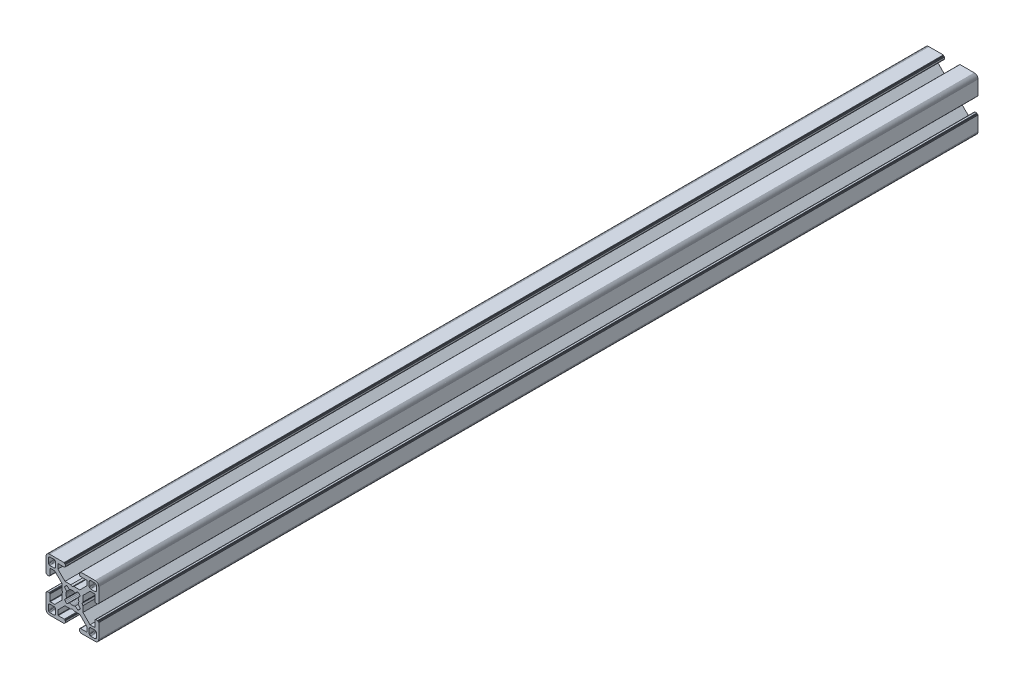
SolidWorks part; units mm, degrees
ref_plane "Front Plane" through (0, 0, 0) normal (0, 0, 1) x (1, 0, 0)
ref_plane "Top Plane" through (0, 0, 0) normal (0, 1, 0) x (1, 0, 0)
ref_plane "Right Plane" through (0, 0, 0) normal (1, 0, 0) x (0, 0, -1)
ref_plane "Plane1" through (0, 0, 0) normal (0, 0, 1) x (1, 0, 0)
sketch "Sketch1" plane through (0, 0, 0) normal (0, 0, 1) x (1, 0, 0)
  line L0 (28.3473, 29.9696) -> (28, 30)
  line L1 (28, 30) -> (19.75, 30)
  line L2 (19.75, 30) -> (19.7153, 29.997)
  line L3 (19.7153, 29.997) -> (19.6816, 29.9879)
  line L4 (19.6816, 29.9879) -> (19.65, 29.9732)
  line L5 (19.65, 29.9732) -> (19.6214, 29.9532)
  line L6 (19.6214, 29.9532) -> (19.5968, 29.9286)
  line L7 (19.5968, 29.9286) -> (19.5768, 29.9)
  line L8 (19.5768, 29.9) -> (19.5621, 29.8684)
  line L9 (19.5621, 29.8684) -> (19.553, 29.8347)
  line L10 (19.553, 29.8347) -> (19.55, 29.8)
  line L11 (19.55, 29.8) -> (19.55, 29.7)
  line L12 (19.55, 29.7) -> (19.547, 29.6653)
  line L13 (19.547, 29.6653) -> (19.5379, 29.6316)
  line L14 (19.5379, 29.6316) -> (19.5232, 29.6)
  line L15 (19.5232, 29.6) -> (19.5032, 29.5714)
  line L16 (19.5032, 29.5714) -> (19.4786, 29.5468)
  line L17 (19.4786, 29.5468) -> (19.45, 29.5268)
  line L18 (19.45, 29.5268) -> (19.4184, 29.5121)
  line L19 (19.4184, 29.5121) -> (19.3847, 29.503)
  line L20 (19.3847, 29.503) -> (19.35, 29.5)
  line L21 (19.35, 29.5) -> (19.25, 29.5)
  line L22 (19.25, 29.5) -> (19.2153, 29.497)
  line L23 (19.2153, 29.497) -> (19.1816, 29.4879)
  line L24 (19.1816, 29.4879) -> (19.15, 29.4732)
  line L25 (19.15, 29.4732) -> (19.1214, 29.4532)
  line L26 (19.1214, 29.4532) -> (19.0968, 29.4286)
  line L27 (19.0968, 29.4286) -> (19.0768, 29.4)
  line L28 (19.0768, 29.4) -> (19.0621, 29.3684)
  line L29 (19.0621, 29.3684) -> (19.053, 29.3347)
  line L30 (19.053, 29.3347) -> (19.05, 29.3)
  line L31 (19.05, 29.3) -> (19.05, 28.4)
  line L32 (19.05, 28.4) -> (19.0591, 28.2958)
  line L33 (19.0591, 28.2958) -> (19.0862, 28.1948)
  line L34 (19.0862, 28.1948) -> (19.1304, 28.1)
  line L35 (19.1304, 28.1) -> (19.1904, 28.0143)
  line L36 (19.1904, 28.0143) -> (19.2643, 27.9404)
  line L37 (19.2643, 27.9404) -> (19.35, 27.8804)
  line L38 (19.35, 27.8804) -> (19.4448, 27.8362)
  line L39 (19.4448, 27.8362) -> (19.5458, 27.8091)
  line L40 (19.5458, 27.8091) -> (19.65, 27.8)
  line L41 (19.65, 27.8) -> (23.05, 27.8)
  line L42 (23.05, 27.8) -> (23.0847, 27.7969)
  line L43 (23.0847, 27.7969) -> (23.1184, 27.7879)
  line L44 (23.1184, 27.7879) -> (23.15, 27.7732)
  line L45 (23.15, 27.7732) -> (23.1786, 27.7532)
  line L46 (23.1786, 27.7532) -> (23.2032, 27.7285)
  line L47 (23.2032, 27.7285) -> (23.2232, 27.7)
  line L48 (23.2232, 27.7) -> (23.2379, 27.6684)
  line L49 (23.2379, 27.6684) -> (23.247, 27.6347)
  line L50 (23.247, 27.6347) -> (23.25, 27.6)
  line L51 (23.25, 27.6) -> (23.25, 25.05)
  line L52 (23.25, 25.05) -> (19.2045, 21)
  line L53 (19.2045, 21) -> (15.9, 21)
  line L54 (15.9, 21) -> (15, 20.4848)
  line L55 (15, 20.4848) -> (14.1, 21)
  line L56 (14.1, 21) -> (10.7955, 21)
  line L57 (10.7955, 21) -> (7.9973, 23.8013)
  line L58 (7.9973, 23.8013) -> (6.75, 25.05)
  line L59 (6.75, 25.05) -> (6.75, 27.6)
  line L60 (6.75, 27.6) -> (6.753, 27.6347)
  line L61 (6.753, 27.6347) -> (6.7621, 27.6684)
  line L62 (6.7621, 27.6684) -> (6.7768, 27.7)
  line L63 (6.7768, 27.7) -> (6.7968, 27.7285)
  line L64 (6.7968, 27.7285) -> (6.8215, 27.7532)
  line L65 (6.8215, 27.7532) -> (6.85, 27.7732)
  line L66 (6.85, 27.7732) -> (6.8816, 27.7879)
  line L67 (6.8816, 27.7879) -> (6.9153, 27.7969)
  line L68 (6.9153, 27.7969) -> (6.95, 27.8)
  line L69 (6.95, 27.8) -> (10.35, 27.8)
  line L70 (10.35, 27.8) -> (10.4542, 27.8091)
  line L71 (10.4542, 27.8091) -> (10.5552, 27.8362)
  line L72 (10.5552, 27.8362) -> (10.65, 27.8804)
  line L73 (10.65, 27.8804) -> (10.7357, 27.9404)
  line L74 (10.7357, 27.9404) -> (10.8096, 28.0143)
  line L75 (10.8096, 28.0143) -> (10.8696, 28.1)
  line L76 (10.8696, 28.1) -> (10.9138, 28.1948)
  line L77 (10.9138, 28.1948) -> (10.9409, 28.2958)
  line L78 (10.9409, 28.2958) -> (10.95, 28.4)
  line L79 (10.95, 28.4) -> (10.95, 29.3)
  line L80 (10.95, 29.3) -> (10.947, 29.3347)
  line L81 (10.947, 29.3347) -> (10.938, 29.3684)
  line L82 (10.938, 29.3684) -> (10.9232, 29.4)
  line L83 (10.9232, 29.4) -> (10.9032, 29.4286)
  line L84 (10.9032, 29.4286) -> (10.8786, 29.4532)
  line L85 (10.8786, 29.4532) -> (10.85, 29.4732)
  line L86 (10.85, 29.4732) -> (10.8184, 29.4879)
  line L87 (10.8184, 29.4879) -> (10.7847, 29.497)
  line L88 (10.7847, 29.497) -> (10.75, 29.5)
  line L89 (10.75, 29.5) -> (10.65, 29.5)
  line L90 (10.65, 29.5) -> (10.6153, 29.503)
  line L91 (10.6153, 29.503) -> (10.5816, 29.5121)
  line L92 (10.5816, 29.5121) -> (10.55, 29.5268)
  line L93 (10.55, 29.5268) -> (10.5214, 29.5468)
  line L94 (10.5214, 29.5468) -> (10.4968, 29.5714)
  line L95 (10.4968, 29.5714) -> (10.4768, 29.6)
  line L96 (10.4768, 29.6) -> (10.4621, 29.6316)
  line L97 (10.4621, 29.6316) -> (10.453, 29.6653)
  line L98 (10.453, 29.6653) -> (10.45, 29.7)
  line L99 (10.45, 29.7) -> (10.45, 29.8)
  line L100 (10.45, 29.8) -> (10.447, 29.8347)
  line L101 (10.447, 29.8347) -> (10.4379, 29.8684)
  line L102 (10.4379, 29.8684) -> (10.4232, 29.9)
  line L103 (10.4232, 29.9) -> (10.4032, 29.9286)
  line L104 (10.4032, 29.9286) -> (10.3786, 29.9532)
  line L105 (10.3786, 29.9532) -> (10.35, 29.9732)
  line L106 (10.35, 29.9732) -> (10.3184, 29.9879)
  line L107 (10.3184, 29.9879) -> (10.2847, 29.997)
  line L108 (10.2847, 29.997) -> (10.25, 30)
  line L109 (10.25, 30) -> (2, 30)
  line L110 (2, 30) -> (1.6527, 29.9696)
  line L111 (1.6527, 29.9696) -> (1.316, 29.8794)
  line L112 (1.316, 29.8794) -> (1, 29.7321)
  line L113 (1, 29.7321) -> (0.7144, 29.5321)
  line L114 (0.7144, 29.5321) -> (0.4679, 29.2856)
  line L115 (0.4679, 29.2856) -> (0.2679, 29)
  line L116 (0.2679, 29) -> (0.1206, 28.684)
  line L117 (0.1206, 28.684) -> (0.0304, 28.3473)
  line L118 (0.0304, 28.3473) -> (0, 28)
  line L119 (0, 28) -> (0, 19.75)
  line L120 (0, 19.75) -> (0.003, 19.7153)
  line L121 (0.003, 19.7153) -> (0.0121, 19.6816)
  line L122 (0.0121, 19.6816) -> (0.0268, 19.65)
  line L123 (0.0268, 19.65) -> (0.0468, 19.6214)
  line L124 (0.0468, 19.6214) -> (0.0714, 19.5968)
  line L125 (0.0714, 19.5968) -> (0.1, 19.5768)
  line L126 (0.1, 19.5768) -> (0.1316, 19.5621)
  line L127 (0.1316, 19.5621) -> (0.1653, 19.553)
  line L128 (0.1653, 19.553) -> (0.2, 19.55)
  line L129 (0.2, 19.55) -> (0.3, 19.55)
  line L130 (0.3, 19.55) -> (0.3347, 19.547)
  line L131 (0.3347, 19.547) -> (0.3684, 19.5379)
  line L132 (0.3684, 19.5379) -> (0.4, 19.5232)
  line L133 (0.4, 19.5232) -> (0.4286, 19.5032)
  line L134 (0.4286, 19.5032) -> (0.4532, 19.4786)
  line L135 (0.4532, 19.4786) -> (0.4732, 19.45)
  line L136 (0.4732, 19.45) -> (0.4879, 19.4184)
  line L137 (0.4879, 19.4184) -> (0.497, 19.3847)
  line L138 (0.497, 19.3847) -> (0.5, 19.35)
  line L139 (0.5, 19.35) -> (0.5, 19.25)
  line L140 (0.5, 19.25) -> (0.503, 19.2153)
  line L141 (0.503, 19.2153) -> (0.5121, 19.1816)
  line L142 (0.5121, 19.1816) -> (0.5268, 19.15)
  line L143 (0.5268, 19.15) -> (0.5468, 19.1214)
  line L144 (0.5468, 19.1214) -> (0.5714, 19.0968)
  line L145 (0.5714, 19.0968) -> (0.6, 19.0768)
  line L146 (0.6, 19.0768) -> (0.6316, 19.0621)
  line L147 (0.6316, 19.0621) -> (0.6653, 19.053)
  line L148 (0.6653, 19.053) -> (0.7, 19.05)
  line L149 (0.7, 19.05) -> (1.6, 19.05)
  line L150 (1.6, 19.05) -> (1.7042, 19.0591)
  line L151 (1.7042, 19.0591) -> (1.8052, 19.0862)
  line L152 (1.8052, 19.0862) -> (1.9, 19.1304)
  line L153 (1.9, 19.1304) -> (1.9857, 19.1904)
  line L154 (1.9857, 19.1904) -> (2.0596, 19.2643)
  line L155 (2.0596, 19.2643) -> (2.1196, 19.35)
  line L156 (2.1196, 19.35) -> (2.1638, 19.4448)
  line L157 (2.1638, 19.4448) -> (2.1909, 19.5458)
  line L158 (2.1909, 19.5458) -> (2.2, 19.65)
  line L159 (2.2, 19.65) -> (2.2, 23.05)
  line L160 (2.2, 23.05) -> (2.203, 23.0847)
  line L161 (2.203, 23.0847) -> (2.2121, 23.1184)
  line L162 (2.2121, 23.1184) -> (2.2268, 23.15)
  line L163 (2.2268, 23.15) -> (2.2468, 23.1786)
  line L164 (2.2468, 23.1786) -> (2.2714, 23.2032)
  line L165 (2.2714, 23.2032) -> (2.3, 23.2232)
  line L166 (2.3, 23.2232) -> (2.3316, 23.2379)
  line L167 (2.3316, 23.2379) -> (2.3653, 23.247)
  line L168 (2.3653, 23.247) -> (2.4, 23.25)
  line L169 (2.4, 23.25) -> (4.95, 23.25)
  line L170 (4.95, 23.25) -> (7.9973, 20.2027)
  line L171 (7.9973, 20.2027) -> (8.9955, 19.2045)
  line L172 (8.9955, 19.2045) -> (8.9955, 15.9)
  line L173 (8.9955, 15.9) -> (9.5151, 15)
  line L174 (9.5151, 15) -> (8.9955, 14.1)
  line L175 (8.9955, 14.1) -> (8.9955, 10.7955)
  line L176 (8.9955, 10.7955) -> (4.95, 6.75)
  line L177 (4.95, 6.75) -> (2.4, 6.75)
  line L178 (2.4, 6.75) -> (2.3653, 6.753)
  line L179 (2.3653, 6.753) -> (2.3316, 6.7621)
  line L180 (2.3316, 6.7621) -> (2.3, 6.7768)
  line L181 (2.3, 6.7768) -> (2.2714, 6.7968)
  line L182 (2.2714, 6.7968) -> (2.2468, 6.8214)
  line L183 (2.2468, 6.8214) -> (2.2268, 6.85)
  line L184 (2.2268, 6.85) -> (2.2121, 6.8816)
  line L185 (2.2121, 6.8816) -> (2.203, 6.9153)
  line L186 (2.203, 6.9153) -> (2.2, 6.95)
  line L187 (2.2, 6.95) -> (2.2, 10.35)
  line L188 (2.2, 10.35) -> (2.1909, 10.4542)
  line L189 (2.1909, 10.4542) -> (2.1638, 10.5552)
  line L190 (2.1638, 10.5552) -> (2.1196, 10.65)
  line L191 (2.1196, 10.65) -> (2.0596, 10.7357)
  line L192 (2.0596, 10.7357) -> (1.9857, 10.8096)
  line L193 (1.9857, 10.8096) -> (1.9, 10.8696)
  line L194 (1.9, 10.8696) -> (1.8052, 10.9138)
  line L195 (1.8052, 10.9138) -> (1.7042, 10.9409)
  line L196 (1.7042, 10.9409) -> (1.6, 10.95)
  line L197 (1.6, 10.95) -> (0.7, 10.95)
  line L198 (0.7, 10.95) -> (0.6653, 10.9469)
  line L199 (0.6653, 10.9469) -> (0.6316, 10.9379)
  line L200 (0.6316, 10.9379) -> (0.6, 10.9232)
  line L201 (0.6, 10.9232) -> (0.5715, 10.9032)
  line L202 (0.5715, 10.9032) -> (0.5468, 10.8785)
  line L203 (0.5468, 10.8785) -> (0.5268, 10.85)
  line L204 (0.5268, 10.85) -> (0.5121, 10.8184)
  line L205 (0.5121, 10.8184) -> (0.503, 10.7847)
  line L206 (0.503, 10.7847) -> (0.5, 10.75)
  line L207 (0.5, 10.75) -> (0.5, 10.65)
  line L208 (0.5, 10.65) -> (0.497, 10.6153)
  line L209 (0.497, 10.6153) -> (0.4879, 10.5816)
  line L210 (0.4879, 10.5816) -> (0.4732, 10.55)
  line L211 (0.4732, 10.55) -> (0.4532, 10.5214)
  line L212 (0.4532, 10.5214) -> (0.4286, 10.4968)
  line L213 (0.4286, 10.4968) -> (0.4, 10.4768)
  line L214 (0.4, 10.4768) -> (0.3684, 10.4621)
  line L215 (0.3684, 10.4621) -> (0.3347, 10.453)
  line L216 (0.3347, 10.453) -> (0.3, 10.45)
  line L217 (0.3, 10.45) -> (0.2, 10.45)
  line L218 (0.2, 10.45) -> (0.1653, 10.447)
  line L219 (0.1653, 10.447) -> (0.1316, 10.4379)
  line L220 (0.1316, 10.4379) -> (0.1, 10.4232)
  line L221 (0.1, 10.4232) -> (0.0714, 10.4032)
  line L222 (0.0714, 10.4032) -> (0.0468, 10.3786)
  line L223 (0.0468, 10.3786) -> (0.0268, 10.35)
  line L224 (0.0268, 10.35) -> (0.0121, 10.3184)
  line L225 (0.0121, 10.3184) -> (0.003, 10.2847)
  line L226 (0.003, 10.2847) -> (0, 10.25)
  line L227 (0, 10.25) -> (0, 2)
  line L228 (0, 2) -> (0.0304, 1.6527)
  line L229 (0.0304, 1.6527) -> (0.1206, 1.316)
  line L230 (0.1206, 1.316) -> (0.2679, 1)
  line L231 (0.2679, 1) -> (0.4679, 0.7144)
  line L232 (0.4679, 0.7144) -> (0.7144, 0.4679)
  line L233 (0.7144, 0.4679) -> (1, 0.2679)
  line L234 (1, 0.2679) -> (1.316, 0.1206)
  line L235 (1.316, 0.1206) -> (1.6527, 0.0304)
  line L236 (1.6527, 0.0304) -> (2, 0)
  line L237 (2, 0) -> (10.25, 0)
  line L238 (10.25, 0) -> (10.2847, 0.003)
  line L239 (10.2847, 0.003) -> (10.3184, 0.0121)
  line L240 (10.3184, 0.0121) -> (10.35, 0.0268)
  line L241 (10.35, 0.0268) -> (10.3786, 0.0468)
  line L242 (10.3786, 0.0468) -> (10.4032, 0.0714)
  line L243 (10.4032, 0.0714) -> (10.4232, 0.1)
  line L244 (10.4232, 0.1) -> (10.4379, 0.1316)
  line L245 (10.4379, 0.1316) -> (10.447, 0.1653)
  line L246 (10.447, 0.1653) -> (10.45, 0.2)
  line L247 (10.45, 0.2) -> (10.45, 0.3)
  line L248 (10.45, 0.3) -> (10.453, 0.3347)
  line L249 (10.453, 0.3347) -> (10.4621, 0.3684)
  line L250 (10.4621, 0.3684) -> (10.4768, 0.4)
  line L251 (10.4768, 0.4) -> (10.4968, 0.4286)
  line L252 (10.4968, 0.4286) -> (10.5214, 0.4532)
  line L253 (10.5214, 0.4532) -> (10.55, 0.4732)
  line L254 (10.55, 0.4732) -> (10.5816, 0.4879)
  line L255 (10.5816, 0.4879) -> (10.6153, 0.497)
  line L256 (10.6153, 0.497) -> (10.65, 0.5)
  line L257 (10.65, 0.5) -> (10.75, 0.5)
  line L258 (10.75, 0.5) -> (10.7847, 0.503)
  line L259 (10.7847, 0.503) -> (10.8184, 0.5121)
  line L260 (10.8184, 0.5121) -> (10.85, 0.5268)
  line L261 (10.85, 0.5268) -> (10.8785, 0.5468)
  line L262 (10.8785, 0.5468) -> (10.9032, 0.5715)
  line L263 (10.9032, 0.5715) -> (10.9232, 0.6)
  line L264 (10.9232, 0.6) -> (10.9379, 0.6316)
  line L265 (10.9379, 0.6316) -> (10.9469, 0.6653)
  line L266 (10.9469, 0.6653) -> (10.95, 0.7)
  line L267 (10.95, 0.7) -> (10.95, 1.6)
  line L268 (10.95, 1.6) -> (10.9409, 1.7042)
  line L269 (10.9409, 1.7042) -> (10.9138, 1.8052)
  line L270 (10.9138, 1.8052) -> (10.8696, 1.9)
  line L271 (10.8696, 1.9) -> (10.8096, 1.9857)
  line L272 (10.8096, 1.9857) -> (10.7357, 2.0596)
  line L273 (10.7357, 2.0596) -> (10.65, 2.1196)
  line L274 (10.65, 2.1196) -> (10.5552, 2.1638)
  line L275 (10.5552, 2.1638) -> (10.4542, 2.1909)
  line L276 (10.4542, 2.1909) -> (10.35, 2.2)
  line L277 (10.35, 2.2) -> (6.95, 2.2)
  line L278 (6.95, 2.2) -> (6.9153, 2.203)
  line L279 (6.9153, 2.203) -> (6.8816, 2.212)
  line L280 (6.8816, 2.212) -> (6.85, 2.2268)
  line L281 (6.85, 2.2268) -> (6.8215, 2.2468)
  line L282 (6.8215, 2.2468) -> (6.7968, 2.2714)
  line L283 (6.7968, 2.2714) -> (6.7768, 2.3)
  line L284 (6.7768, 2.3) -> (6.7621, 2.3316)
  line L285 (6.7621, 2.3316) -> (6.753, 2.3653)
  line L286 (6.753, 2.3653) -> (6.75, 2.4)
  line L287 (6.75, 2.4) -> (6.75, 4.95)
  line L288 (6.75, 4.95) -> (9.7875, 7.9908)
  line L289 (9.7875, 7.9908) -> (10.7955, 9)
  line L290 (10.7955, 9) -> (14.1, 9)
  line L291 (14.1, 9) -> (15, 9.5151)
  line L292 (15, 9.5151) -> (15.9, 9)
  line L293 (15.9, 9) -> (19.2045, 9)
  line L294 (19.2045, 9) -> (20.2126, 7.9908)
  line L295 (20.2126, 7.9908) -> (23.25, 4.95)
  line L296 (23.25, 4.95) -> (23.25, 2.4)
  line L297 (23.25, 2.4) -> (23.247, 2.3653)
  line L298 (23.247, 2.3653) -> (23.2379, 2.3316)
  line L299 (23.2379, 2.3316) -> (23.2232, 2.3)
  line L300 (23.2232, 2.3) -> (23.2032, 2.2714)
  line L301 (23.2032, 2.2714) -> (23.1786, 2.2468)
  line L302 (23.1786, 2.2468) -> (23.15, 2.2268)
  line L303 (23.15, 2.2268) -> (23.1184, 2.212)
  line L304 (23.1184, 2.212) -> (23.0847, 2.203)
  line L305 (23.0847, 2.203) -> (23.05, 2.2)
  line L306 (23.05, 2.2) -> (19.65, 2.2)
  line L307 (19.65, 2.2) -> (19.5458, 2.1909)
  line L308 (19.5458, 2.1909) -> (19.4448, 2.1638)
  line L309 (19.4448, 2.1638) -> (19.35, 2.1196)
  line L310 (19.35, 2.1196) -> (19.2643, 2.0596)
  line L311 (19.2643, 2.0596) -> (19.1904, 1.9857)
  line L312 (19.1904, 1.9857) -> (19.1304, 1.9)
  line L313 (19.1304, 1.9) -> (19.0862, 1.8052)
  line L314 (19.0862, 1.8052) -> (19.0591, 1.7042)
  line L315 (19.0591, 1.7042) -> (19.05, 1.6)
  line L316 (19.05, 1.6) -> (19.05, 0.7)
  line L317 (19.05, 0.7) -> (19.053, 0.6653)
  line L318 (19.053, 0.6653) -> (19.0621, 0.6316)
  line L319 (19.0621, 0.6316) -> (19.0768, 0.6)
  line L320 (19.0768, 0.6) -> (19.0968, 0.5714)
  line L321 (19.0968, 0.5714) -> (19.1214, 0.5468)
  line L322 (19.1214, 0.5468) -> (19.15, 0.5268)
  line L323 (19.15, 0.5268) -> (19.1816, 0.5121)
  line L324 (19.1816, 0.5121) -> (19.2153, 0.503)
  line L325 (19.2153, 0.503) -> (19.25, 0.5)
  line L326 (19.25, 0.5) -> (19.35, 0.5)
  line L327 (19.35, 0.5) -> (19.3847, 0.497)
  line L328 (19.3847, 0.497) -> (19.4184, 0.4879)
  line L329 (19.4184, 0.4879) -> (19.45, 0.4732)
  line L330 (19.45, 0.4732) -> (19.4786, 0.4532)
  line L331 (19.4786, 0.4532) -> (19.5032, 0.4286)
  line L332 (19.5032, 0.4286) -> (19.5232, 0.4)
  line L333 (19.5232, 0.4) -> (19.5379, 0.3684)
  line L334 (19.5379, 0.3684) -> (19.547, 0.3347)
  line L335 (19.547, 0.3347) -> (19.55, 0.3)
  line L336 (19.55, 0.3) -> (19.55, 0.2)
  line L337 (19.55, 0.2) -> (19.553, 0.1653)
  line L338 (19.553, 0.1653) -> (19.5621, 0.1316)
  line L339 (19.5621, 0.1316) -> (19.5768, 0.1)
  line L340 (19.5768, 0.1) -> (19.5968, 0.0714)
  line L341 (19.5968, 0.0714) -> (19.6214, 0.0468)
  line L342 (19.6214, 0.0468) -> (19.65, 0.0268)
  line L343 (19.65, 0.0268) -> (19.6816, 0.0121)
  line L344 (19.6816, 0.0121) -> (19.7153, 0.003)
  line L345 (19.7153, 0.003) -> (19.75, 0)
  line L346 (19.75, 0) -> (28, 0)
  line L347 (28, 0) -> (28.3473, 0.0304)
  line L348 (28.3473, 0.0304) -> (28.684, 0.1206)
  line L349 (28.684, 0.1206) -> (29, 0.2679)
  line L350 (29, 0.2679) -> (29.2856, 0.4679)
  line L351 (29.2856, 0.4679) -> (29.5321, 0.7144)
  line L352 (29.5321, 0.7144) -> (29.7321, 1)
  line L353 (29.7321, 1) -> (29.8794, 1.316)
  line L354 (29.8794, 1.316) -> (29.9696, 1.6527)
  line L355 (29.9696, 1.6527) -> (30, 2)
  line L356 (30, 2) -> (30, 10.25)
  line L357 (30, 10.25) -> (29.997, 10.2847)
  line L358 (29.997, 10.2847) -> (29.988, 10.3184)
  line L359 (29.988, 10.3184) -> (29.9732, 10.35)
  line L360 (29.9732, 10.35) -> (29.9532, 10.3785)
  line L361 (29.9532, 10.3785) -> (29.9286, 10.4032)
  line L362 (29.9286, 10.4032) -> (29.9, 10.4232)
  line L363 (29.9, 10.4232) -> (29.8684, 10.4379)
  line L364 (29.8684, 10.4379) -> (29.8347, 10.447)
  line L365 (29.8347, 10.447) -> (29.8, 10.45)
  line L366 (29.8, 10.45) -> (29.7, 10.45)
  line L367 (29.7, 10.45) -> (29.6649, 10.4534)
  line L368 (29.6649, 10.4534) -> (29.6312, 10.4624)
  line L369 (29.6312, 10.4624) -> (29.5996, 10.4772)
  line L370 (29.5996, 10.4772) -> (29.5711, 10.4972)
  line L371 (29.5711, 10.4972) -> (29.5464, 10.5218)
  line L372 (29.5464, 10.5218) -> (29.5264, 10.5504)
  line L373 (29.5264, 10.5504) -> (29.5117, 10.582)
  line L374 (29.5117, 10.582) -> (29.5027, 10.6156)
  line L375 (29.5027, 10.6156) -> (29.4996, 10.6504)
  line L376 (29.4996, 10.6504) -> (29.4996, 10.7504)
  line L377 (29.4996, 10.7504) -> (29.497, 10.7847)
  line L378 (29.497, 10.7847) -> (29.4879, 10.8184)
  line L379 (29.4879, 10.8184) -> (29.4732, 10.85)
  line L380 (29.4732, 10.85) -> (29.4532, 10.8785)
  line L381 (29.4532, 10.8785) -> (29.4286, 10.9032)
  line L382 (29.4286, 10.9032) -> (29.4, 10.9232)
  line L383 (29.4, 10.9232) -> (29.3684, 10.9379)
  line L384 (29.3684, 10.9379) -> (29.3347, 10.9469)
  line L385 (29.3347, 10.9469) -> (29.3, 10.95)
  line L386 (29.3, 10.95) -> (28.4, 10.95)
  line L387 (28.4, 10.95) -> (28.2958, 10.9409)
  line L388 (28.2958, 10.9409) -> (28.1948, 10.9138)
  line L389 (28.1948, 10.9138) -> (28.1, 10.8696)
  line L390 (28.1, 10.8696) -> (28.0143, 10.8096)
  line L391 (28.0143, 10.8096) -> (27.9404, 10.7357)
  line L392 (27.9404, 10.7357) -> (27.8804, 10.65)
  line L393 (27.8804, 10.65) -> (27.8362, 10.5552)
  line L394 (27.8362, 10.5552) -> (27.8091, 10.4542)
  line L395 (27.8091, 10.4542) -> (27.8, 10.35)
  line L396 (27.8, 10.35) -> (27.8, 6.95)
  line L397 (27.8, 6.95) -> (27.797, 6.9153)
  line L398 (27.797, 6.9153) -> (27.7879, 6.8816)
  line L399 (27.7879, 6.8816) -> (27.7732, 6.85)
  line L400 (27.7732, 6.85) -> (27.7532, 6.8214)
  line L401 (27.7532, 6.8214) -> (27.7286, 6.7968)
  line L402 (27.7286, 6.7968) -> (27.7, 6.7768)
  line L403 (27.7, 6.7768) -> (27.6684, 6.7621)
  line L404 (27.6684, 6.7621) -> (27.6347, 6.753)
  line L405 (27.6347, 6.753) -> (27.6, 6.75)
  line L406 (27.6, 6.75) -> (25.05, 6.75)
  line L407 (25.05, 6.75) -> (23.8092, 7.9908)
  line L408 (23.8092, 7.9908) -> (21.0045, 10.7955)
  line L409 (21.0045, 10.7955) -> (21.0045, 14.1)
  line L410 (21.0045, 14.1) -> (20.4849, 15)
  line L411 (20.4849, 15) -> (21.0045, 15.9)
  line L412 (21.0045, 15.9) -> (21.0045, 19.2045)
  line L413 (21.0045, 19.2045) -> (25.05, 23.25)
  line L414 (25.05, 23.25) -> (27.6, 23.25)
  line L415 (27.6, 23.25) -> (27.6347, 23.247)
  line L416 (27.6347, 23.247) -> (27.6684, 23.2379)
  line L417 (27.6684, 23.2379) -> (27.7, 23.2232)
  line L418 (27.7, 23.2232) -> (27.7286, 23.2032)
  line L419 (27.7286, 23.2032) -> (27.7532, 23.1786)
  line L420 (27.7532, 23.1786) -> (27.7732, 23.15)
  line L421 (27.7732, 23.15) -> (27.7879, 23.1184)
  line L422 (27.7879, 23.1184) -> (27.797, 23.0847)
  line L423 (27.797, 23.0847) -> (27.8, 23.05)
  line L424 (27.8, 23.05) -> (27.8, 19.65)
  line L425 (27.8, 19.65) -> (27.8091, 19.5458)
  line L426 (27.8091, 19.5458) -> (27.8362, 19.4448)
  line L427 (27.8362, 19.4448) -> (27.8804, 19.35)
  line L428 (27.8804, 19.35) -> (27.9404, 19.2643)
  line L429 (27.9404, 19.2643) -> (28.0143, 19.1904)
  line L430 (28.0143, 19.1904) -> (28.1, 19.1304)
  line L431 (28.1, 19.1304) -> (28.1948, 19.0862)
  line L432 (28.1948, 19.0862) -> (28.2958, 19.0591)
  line L433 (28.2958, 19.0591) -> (28.4, 19.05)
  line L434 (28.4, 19.05) -> (29.3, 19.05)
  line L435 (29.3, 19.05) -> (29.3347, 19.053)
  line L436 (29.3347, 19.053) -> (29.3684, 19.0621)
  line L437 (29.3684, 19.0621) -> (29.4, 19.0768)
  line L438 (29.4, 19.0768) -> (29.4282, 19.0971)
  line L439 (29.4282, 19.0971) -> (29.4528, 19.1218)
  line L440 (29.4528, 19.1218) -> (29.4728, 19.1504)
  line L441 (29.4728, 19.1504) -> (29.4876, 19.182)
  line L442 (29.4876, 19.182) -> (29.4966, 19.2156)
  line L443 (29.4966, 19.2156) -> (29.4996, 19.2504)
  line L444 (29.4996, 19.2504) -> (29.4996, 19.3504)
  line L445 (29.4996, 19.3504) -> (29.5027, 19.3851)
  line L446 (29.5027, 19.3851) -> (29.5117, 19.4188)
  line L447 (29.5117, 19.4188) -> (29.5264, 19.4504)
  line L448 (29.5264, 19.4504) -> (29.5464, 19.4789)
  line L449 (29.5464, 19.4789) -> (29.5711, 19.5036)
  line L450 (29.5711, 19.5036) -> (29.5996, 19.5236)
  line L451 (29.5996, 19.5236) -> (29.6312, 19.5383)
  line L452 (29.6312, 19.5383) -> (29.6649, 19.5473)
  line L453 (29.6649, 19.5473) -> (29.7, 19.55)
  line L454 (29.7, 19.55) -> (29.8, 19.55)
  line L455 (29.8, 19.55) -> (29.8347, 19.553)
  line L456 (29.8347, 19.553) -> (29.8684, 19.5621)
  line L457 (29.8684, 19.5621) -> (29.9, 19.5768)
  line L458 (29.9, 19.5768) -> (29.9286, 19.5968)
  line L459 (29.9286, 19.5968) -> (29.9532, 19.6214)
  line L460 (29.9532, 19.6214) -> (29.9732, 19.65)
  line L461 (29.9732, 19.65) -> (29.9879, 19.6816)
  line L462 (29.9879, 19.6816) -> (29.997, 19.7153)
  line L463 (29.997, 19.7153) -> (30, 19.75)
  line L464 (30, 19.75) -> (30, 28)
  line L465 (30, 28) -> (29.9696, 28.3473)
  line L466 (29.9696, 28.3473) -> (29.8794, 28.684)
  line L467 (29.8794, 28.684) -> (29.7321, 29)
  line L468 (29.7321, 29) -> (29.5321, 29.2856)
  line L469 (29.5321, 29.2856) -> (29.2856, 29.5321)
  line L470 (29.2856, 29.5321) -> (29, 29.7321)
  line L471 (29, 29.7321) -> (28.684, 29.8794)
  line L472 (28.684, 29.8794) -> (28.3473, 29.9696)
  line L473 (1.3, 25.5) -> (1.3, 27.7)
  line L474 (1.3, 27.7) -> (1.3123, 27.8564)
  line L475 (1.3123, 27.8564) -> (1.3489, 28.009)
  line L476 (1.3489, 28.009) -> (1.409, 28.154)
  line L477 (1.409, 28.154) -> (1.491, 28.2878)
  line L478 (1.491, 28.2878) -> (1.5929, 28.4071)
  line L479 (1.5929, 28.4071) -> (1.7122, 28.509)
  line L480 (1.7122, 28.509) -> (1.846, 28.591)
  line L481 (1.846, 28.591) -> (1.991, 28.6511)
  line L482 (1.991, 28.6511) -> (2.1436, 28.6877)
  line L483 (2.1436, 28.6877) -> (2.3, 28.7)
  line L484 (2.3, 28.7) -> (4.5, 28.7)
  line L485 (4.5, 28.7) -> (4.6564, 28.6877)
  line L486 (4.6564, 28.6877) -> (4.809, 28.6511)
  line L487 (4.809, 28.6511) -> (4.954, 28.591)
  line L488 (4.954, 28.591) -> (5.0878, 28.509)
  line L489 (5.0878, 28.509) -> (5.2071, 28.4071)
  line L490 (5.2071, 28.4071) -> (5.309, 28.2878)
  line L491 (5.309, 28.2878) -> (5.391, 28.154)
  line L492 (5.391, 28.154) -> (5.4511, 28.009)
  line L493 (5.4511, 28.009) -> (5.4877, 27.8564)
  line L494 (5.4877, 27.8564) -> (5.5, 27.7)
  line L495 (5.5, 27.7) -> (5.5, 25.5)
  line L496 (5.5, 25.5) -> (5.4877, 25.3436)
  line L497 (5.4877, 25.3436) -> (5.4511, 25.191)
  line L498 (5.4511, 25.191) -> (5.391, 25.046)
  line L499 (5.391, 25.046) -> (5.309, 24.9122)
  line L500 (5.309, 24.9122) -> (5.2071, 24.7929)
  line L501 (5.2071, 24.7929) -> (5.0878, 24.691)
  line L502 (5.0878, 24.691) -> (4.954, 24.609)
  line L503 (4.954, 24.609) -> (4.809, 24.5489)
  line L504 (4.809, 24.5489) -> (4.6564, 24.5123)
  line L505 (4.6564, 24.5123) -> (4.5, 24.5)
  line L506 (4.5, 24.5) -> (2.3, 24.5)
  line L507 (2.3, 24.5) -> (2.1436, 24.5123)
  line L508 (2.1436, 24.5123) -> (1.991, 24.5489)
  line L509 (1.991, 24.5489) -> (1.846, 24.609)
  line L510 (1.846, 24.609) -> (1.7122, 24.691)
  line L511 (1.7122, 24.691) -> (1.5929, 24.7929)
  line L512 (1.5929, 24.7929) -> (1.491, 24.9122)
  line L513 (1.491, 24.9122) -> (1.409, 25.046)
  line L514 (1.409, 25.046) -> (1.3489, 25.191)
  line L515 (1.3489, 25.191) -> (1.3123, 25.3436)
  line L516 (1.3123, 25.3436) -> (1.3, 25.5)
  line L517 (25.3436, 28.6877) -> (25.5, 28.7)
  line L518 (25.5, 28.7) -> (27.7, 28.7)
  line L519 (27.7, 28.7) -> (27.8564, 28.6877)
  line L520 (27.8564, 28.6877) -> (28.009, 28.6511)
  line L521 (28.009, 28.6511) -> (28.154, 28.591)
  line L522 (28.154, 28.591) -> (28.2878, 28.509)
  line L523 (28.2878, 28.509) -> (28.4071, 28.4071)
  line L524 (28.4071, 28.4071) -> (28.509, 28.2878)
  line L525 (28.509, 28.2878) -> (28.591, 28.154)
  line L526 (28.591, 28.154) -> (28.6511, 28.009)
  line L527 (28.6511, 28.009) -> (28.6877, 27.8564)
  line L528 (28.6877, 27.8564) -> (28.7, 27.7)
  line L529 (28.7, 27.7) -> (28.7, 25.5)
  line L530 (28.7, 25.5) -> (28.6877, 25.3436)
  line L531 (28.6877, 25.3436) -> (28.6511, 25.191)
  line L532 (28.6511, 25.191) -> (28.591, 25.046)
  line L533 (28.591, 25.046) -> (28.509, 24.9122)
  line L534 (28.509, 24.9122) -> (28.4071, 24.7929)
  line L535 (28.4071, 24.7929) -> (28.2878, 24.691)
  line L536 (28.2878, 24.691) -> (28.154, 24.609)
  line L537 (28.154, 24.609) -> (28.009, 24.5489)
  line L538 (28.009, 24.5489) -> (27.8564, 24.5123)
  line L539 (27.8564, 24.5123) -> (27.7, 24.5)
  line L540 (27.7, 24.5) -> (25.5, 24.5)
  line L541 (25.5, 24.5) -> (25.3436, 24.5123)
  line L542 (25.3436, 24.5123) -> (25.191, 24.5489)
  line L543 (25.191, 24.5489) -> (25.046, 24.609)
  line L544 (25.046, 24.609) -> (24.9122, 24.691)
  line L545 (24.9122, 24.691) -> (24.7929, 24.7929)
  line L546 (24.7929, 24.7929) -> (24.691, 24.9122)
  line L547 (24.691, 24.9122) -> (24.609, 25.046)
  line L548 (24.609, 25.046) -> (24.5489, 25.191)
  line L549 (24.5489, 25.191) -> (24.5123, 25.3436)
  line L550 (24.5123, 25.3436) -> (24.5, 25.5)
  line L551 (24.5, 25.5) -> (24.5, 27.7)
  line L552 (24.5, 27.7) -> (24.5123, 27.8564)
  line L553 (24.5123, 27.8564) -> (24.5489, 28.009)
  line L554 (24.5489, 28.009) -> (24.609, 28.154)
  line L555 (24.609, 28.154) -> (24.691, 28.2878)
  line L556 (24.691, 28.2878) -> (24.7929, 28.4071)
  line L557 (24.7929, 28.4071) -> (24.9122, 28.509)
  line L558 (24.9122, 28.509) -> (25.046, 28.591)
  line L559 (25.046, 28.591) -> (25.191, 28.6511)
  line L560 (25.191, 28.6511) -> (25.3436, 28.6877)
  line L561 (15, 18.65) -> (15.55, 18.6083)
  line L562 (15.55, 18.6083) -> (16.0875, 18.4842)
  line L563 (16.0875, 18.4842) -> (16.6001, 18.2806)
  line L564 (16.6001, 18.2806) -> (18.1359, 19.5184)
  line L565 (18.1359, 19.5184) -> (18.645, 19.1187)
  line L566 (18.645, 19.1187) -> (19.1036, 18.6621)
  line L567 (19.1036, 18.6621) -> (19.5053, 18.1547)
  line L568 (19.5053, 18.1547) -> (18.2806, 16.6001)
  line L569 (18.2806, 16.6001) -> (18.4842, 16.0875)
  line L570 (18.4842, 16.0875) -> (18.6083, 15.55)
  line L571 (18.6083, 15.55) -> (18.65, 15)
  line L572 (18.65, 15) -> (18.6083, 14.45)
  line L573 (18.6083, 14.45) -> (18.4842, 13.9125)
  line L574 (18.4842, 13.9125) -> (18.2806, 13.3999)
  line L575 (18.2806, 13.3999) -> (19.5053, 11.8453)
  line L576 (19.5053, 11.8453) -> (19.1036, 11.3379)
  line L577 (19.1036, 11.3379) -> (18.645, 10.8813)
  line L578 (18.645, 10.8813) -> (18.1359, 10.4816)
  line L579 (18.1359, 10.4816) -> (16.6001, 11.7194)
  line L580 (16.6001, 11.7194) -> (16.0875, 11.5158)
  line L581 (16.0875, 11.5158) -> (15.55, 11.3917)
  line L582 (15.55, 11.3917) -> (15, 11.35)
  line L583 (15, 11.35) -> (14.45, 11.3917)
  line L584 (14.45, 11.3917) -> (13.9125, 11.5158)
  line L585 (13.9125, 11.5158) -> (13.3999, 11.7194)
  line L586 (13.3999, 11.7194) -> (11.8641, 10.4816)
  line L587 (11.8641, 10.4816) -> (11.355, 10.8813)
  line L588 (11.355, 10.8813) -> (10.8964, 11.3379)
  line L589 (10.8964, 11.3379) -> (10.4947, 11.8453)
  line L590 (10.4947, 11.8453) -> (11.7194, 13.3999)
  line L591 (11.7194, 13.3999) -> (11.5158, 13.9125)
  line L592 (11.5158, 13.9125) -> (11.3917, 14.45)
  line L593 (11.3917, 14.45) -> (11.35, 15)
  line L594 (11.35, 15) -> (11.3917, 15.55)
  line L595 (11.3917, 15.55) -> (11.5158, 16.0875)
  line L596 (11.5158, 16.0875) -> (11.7194, 16.6001)
  line L597 (11.7194, 16.6001) -> (10.4947, 18.1547)
  line L598 (10.4947, 18.1547) -> (10.8964, 18.6621)
  line L599 (10.8964, 18.6621) -> (11.355, 19.1187)
  line L600 (11.355, 19.1187) -> (11.8641, 19.5184)
  line L601 (11.8641, 19.5184) -> (13.3999, 18.2806)
  line L602 (13.3999, 18.2806) -> (13.9125, 18.4842)
  line L603 (13.9125, 18.4842) -> (14.45, 18.6083)
  line L604 (14.45, 18.6083) -> (15, 18.65)
  line L605 (4.5, 1.3) -> (2.3, 1.3)
  line L606 (2.3, 1.3) -> (2.1436, 1.3123)
  line L607 (2.1436, 1.3123) -> (1.991, 1.3489)
  line L608 (1.991, 1.3489) -> (1.846, 1.409)
  line L609 (1.846, 1.409) -> (1.7122, 1.491)
  line L610 (1.7122, 1.491) -> (1.5929, 1.5929)
  line L611 (1.5929, 1.5929) -> (1.491, 1.7122)
  line L612 (1.491, 1.7122) -> (1.409, 1.846)
  line L613 (1.409, 1.846) -> (1.3489, 1.991)
  line L614 (1.3489, 1.991) -> (1.3123, 2.1436)
  line L615 (1.3123, 2.1436) -> (1.3, 2.3)
  line L616 (1.3, 2.3) -> (1.3, 4.5)
  line L617 (1.3, 4.5) -> (1.3123, 4.6564)
  line L618 (1.3123, 4.6564) -> (1.3489, 4.809)
  line L619 (1.3489, 4.809) -> (1.409, 4.954)
  line L620 (1.409, 4.954) -> (1.491, 5.0878)
  line L621 (1.491, 5.0878) -> (1.5929, 5.2071)
  line L622 (1.5929, 5.2071) -> (1.7122, 5.309)
  line L623 (1.7122, 5.309) -> (1.846, 5.391)
  line L624 (1.846, 5.391) -> (1.991, 5.4511)
  line L625 (1.991, 5.4511) -> (2.1436, 5.4877)
  line L626 (2.1436, 5.4877) -> (2.3, 5.5)
  line L627 (2.3, 5.5) -> (4.5, 5.5)
  line L628 (4.5, 5.5) -> (4.6564, 5.4877)
  line L629 (4.6564, 5.4877) -> (4.809, 5.4511)
  line L630 (4.809, 5.4511) -> (4.954, 5.391)
  line L631 (4.954, 5.391) -> (5.0878, 5.309)
  line L632 (5.0878, 5.309) -> (5.2071, 5.2071)
  line L633 (5.2071, 5.2071) -> (5.309, 5.0878)
  line L634 (5.309, 5.0878) -> (5.391, 4.954)
  line L635 (5.391, 4.954) -> (5.4511, 4.809)
  line L636 (5.4511, 4.809) -> (5.4877, 4.6564)
  line L637 (5.4877, 4.6564) -> (5.5, 4.5)
  line L638 (5.5, 4.5) -> (5.5, 2.3)
  line L639 (5.5, 2.3) -> (5.4877, 2.1436)
  line L640 (5.4877, 2.1436) -> (5.4511, 1.991)
  line L641 (5.4511, 1.991) -> (5.391, 1.846)
  line L642 (5.391, 1.846) -> (5.309, 1.7122)
  line L643 (5.309, 1.7122) -> (5.2071, 1.5929)
  line L644 (5.2071, 1.5929) -> (5.0878, 1.491)
  line L645 (5.0878, 1.491) -> (4.954, 1.409)
  line L646 (4.954, 1.409) -> (4.809, 1.3489)
  line L647 (4.809, 1.3489) -> (4.6564, 1.3123)
  line L648 (4.6564, 1.3123) -> (4.5, 1.3)
  line L649 (27.7, 1.3) -> (25.5, 1.3)
  line L650 (25.5, 1.3) -> (25.3436, 1.3123)
  line L651 (25.3436, 1.3123) -> (25.191, 1.3489)
  line L652 (25.191, 1.3489) -> (25.046, 1.409)
  line L653 (25.046, 1.409) -> (24.9122, 1.491)
  line L654 (24.9122, 1.491) -> (24.7929, 1.5929)
  line L655 (24.7929, 1.5929) -> (24.691, 1.7122)
  line L656 (24.691, 1.7122) -> (24.609, 1.846)
  line L657 (24.609, 1.846) -> (24.5489, 1.991)
  line L658 (24.5489, 1.991) -> (24.5123, 2.1436)
  line L659 (24.5123, 2.1436) -> (24.5, 2.3)
  line L660 (24.5, 2.3) -> (24.5, 4.5)
  line L661 (24.5, 4.5) -> (24.5123, 4.6564)
  line L662 (24.5123, 4.6564) -> (24.5489, 4.809)
  line L663 (24.5489, 4.809) -> (24.609, 4.954)
  line L664 (24.609, 4.954) -> (24.691, 5.0878)
  line L665 (24.691, 5.0878) -> (24.7929, 5.2071)
  line L666 (24.7929, 5.2071) -> (24.9122, 5.309)
  line L667 (24.9122, 5.309) -> (25.046, 5.391)
  line L668 (25.046, 5.391) -> (25.191, 5.4511)
  line L669 (25.191, 5.4511) -> (25.3436, 5.4877)
  line L670 (25.3436, 5.4877) -> (25.5, 5.5)
  line L671 (25.5, 5.5) -> (27.7, 5.5)
  line L672 (27.7, 5.5) -> (27.8564, 5.4877)
  line L673 (27.8564, 5.4877) -> (28.009, 5.4511)
  line L674 (28.009, 5.4511) -> (28.154, 5.391)
  line L675 (28.154, 5.391) -> (28.2878, 5.309)
  line L676 (28.2878, 5.309) -> (28.4071, 5.2071)
  line L677 (28.4071, 5.2071) -> (28.509, 5.0878)
  line L678 (28.509, 5.0878) -> (28.591, 4.954)
  line L679 (28.591, 4.954) -> (28.6511, 4.809)
  line L680 (28.6511, 4.809) -> (28.6877, 4.6564)
  line L681 (28.6877, 4.6564) -> (28.7, 4.5)
  line L682 (28.7, 4.5) -> (28.7, 2.3)
  line L683 (28.7, 2.3) -> (28.6877, 2.1436)
  line L684 (28.6877, 2.1436) -> (28.6511, 1.991)
  line L685 (28.6511, 1.991) -> (28.591, 1.846)
  line L686 (28.591, 1.846) -> (28.509, 1.7122)
  line L687 (28.509, 1.7122) -> (28.4071, 1.5929)
  line L688 (28.4071, 1.5929) -> (28.2878, 1.491)
  line L689 (28.2878, 1.491) -> (28.154, 1.409)
  line L690 (28.154, 1.409) -> (28.009, 1.3489)
  line L691 (28.009, 1.3489) -> (27.8564, 1.3123)
  line L692 (27.8564, 1.3123) -> (27.7, 1.3)
extrude "Boss-Extrude1" add sketch "Sketch1" against normal blind 500
